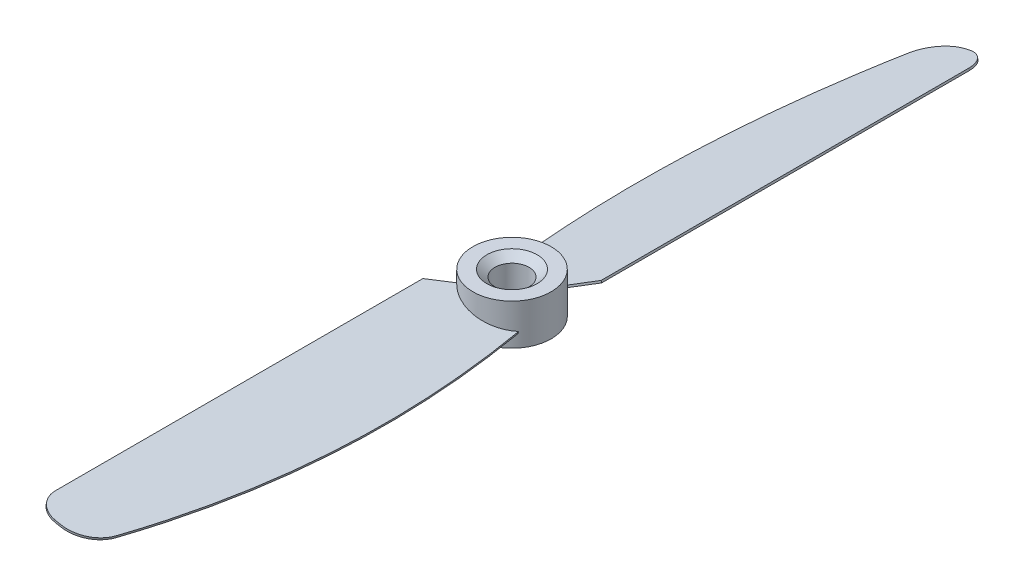
SolidWorks part; units mm, degrees
ref_plane "Front Plane" through (0, 0, 0) normal (0, 0, 1) x (1, 0, 0)
ref_plane "Top Plane" through (0, 0, 0) normal (0, 1, 0) x (1, 0, 0)
ref_plane "Right Plane" through (0, 0, 0) normal (1, 0, 0) x (0, 0, -1)
sketch "Sketch1" plane through (0, 0, 0) normal (0, 1, 0) x (1, 0, 0)
  circle A0 centre (0, 0) radius 5.75
  dimension "D1" = 11.5
extrude "Boss-Extrude1" add sketch "Sketch1" along normal mid plane 6
sketch "Sketch2" plane through (0, 0, 0) normal (0, 0, 1) x (1, 0, 0)
  line L0 (-5.75, 1.3275) -> (5.75, -1.3275) construction
  line L1 (-5.75, 3) -> (-5.75, -3) construction
  line L2 (5.75, -3) -> (5.75, 3) construction
  line L3 (-5.75, -3) -> (5.75, -3) construction
  dimension "D1" = 13
ref_plane "Plane1" through (0, 0, 0) normal (-0.225, -0.9744, 0) x (0.9744, -0.225, 0)
sketch "Sketch3" plane through (0, 0, 0) normal (-0.225, -0.9744, 0) x (0.9744, -0.225, 0)
  line L0 (-3.8421, 3.4017) -> (-6.8781, 6.4377)
  line L1 (-6.8781, 6.4377) -> (-6.8781, 60.5)
  line L2 (-3.8781, 63.5) -> (-3.1931, 63.5)
  arc A0 (1.6612, 59.698) -> (-3.1931, 63.5) centre (-3.1931, 58.5) ccw
  arc A1 (-6.8781, 60.5) -> (-3.8781, 63.5) centre (-3.8781, 60.5) cw
  spline S0 degree 2 poles (-3.8421, 3.4017) (0.4068, 7.3007) (4.405, 2.2535) knots 0 0 0 1 1 1
  spline S1 degree 2 poles (1.6612, 59.698) (9.0309, 31.3131) (4.405, 2.2535) knots 0 0 0 1 1 1
  dimension "D3" = 5
  dimension "D4" = 3
extrude "Boss-Extrude2" add sketch "Sketch3" along normal mid plane 0.3
pattern_circular "CirPattern1" count 2 over 360 about axis through (0, 3, 0) along (0, -1, 0) of "Boss-Extrude2"
sketch "Sketch4" plane through (0, -3, 0) normal (0, -1, 0) x (1, 0, 0)
  circle A0 centre (0, 0) radius 2.5
  dimension "D1" = 5
extrude "Cut-Extrude1" cut sketch "Sketch4" against normal through all
chamfer "Chamfer1" distance 1 angle 50 2 edges at (0, -3, -2.5) (0, 3, -2.5)
